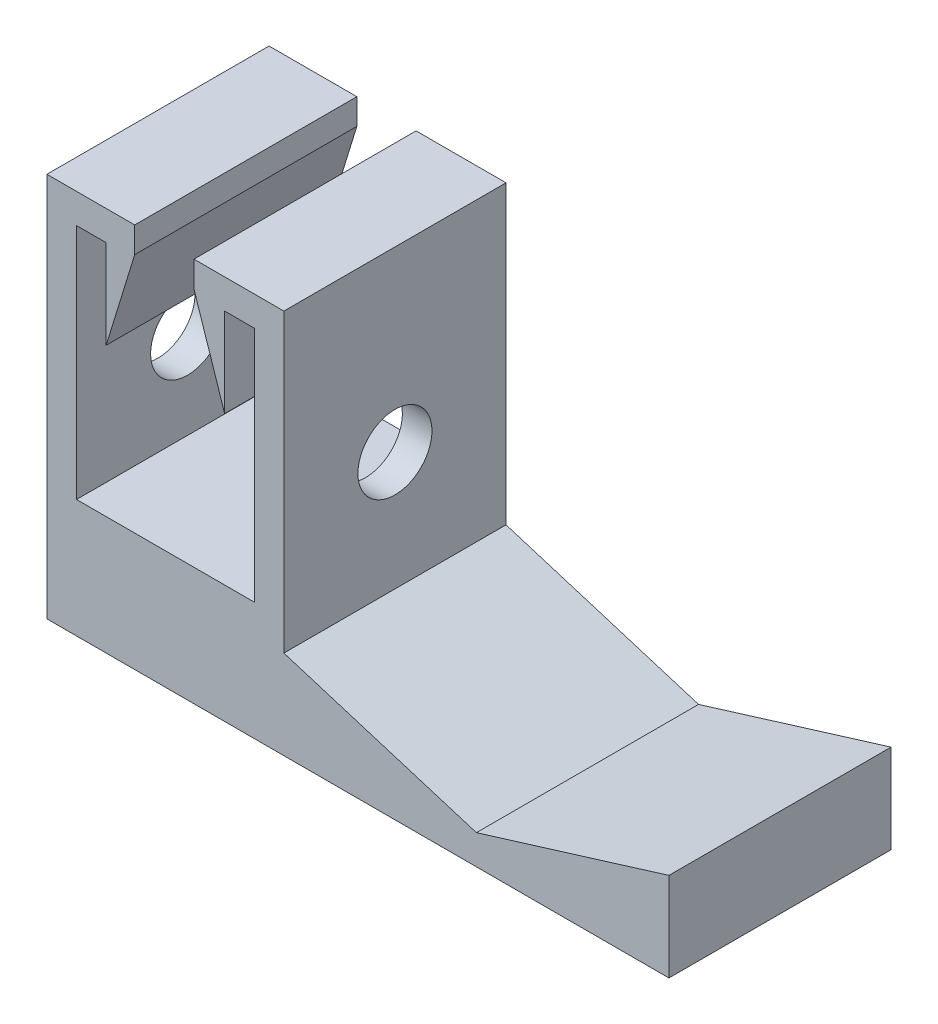
SolidWorks part; units mm, degrees
ref_plane "Front Plane" through (0, 0, 0) normal (0, 0, 1) x (1, 0, 0)
ref_plane "Top Plane" through (0, 0, 0) normal (0, 1, 0) x (1, 0, 0)
ref_plane "Right Plane" through (0, 0, 0) normal (1, 0, 0) x (0, 0, -1)
sketch "Sketch1" plane through (0, 0, 0) normal (0, 0, 1) x (1, 0, 0)
  line L0 (-105, 0) -> (105, 0)
  line L1 (-105, 0) -> (-105, 130)
  line L2 (105, 0) -> (105, 30)
  line L3 (105, 30) -> (40, 10)
  line L4 (40, 10) -> (-25, 30)
  line L5 (-25, 30) -> (-25, 130)
  line L6 (-25, 130) -> (-55.3655, 130)
  line L7 (-55.3655, 130) -> (-55.3655, 121.3121)
  line L8 (-55.3655, 121.3121) -> (-45, 90)
  line L9 (-45, 90) -> (-45, 120)
  line L10 (-45, 120) -> (-35, 120)
  line L11 (-35, 120) -> (-35, 39.9092)
  line L12 (-85, 120) -> (-95, 120)
  line L13 (-85, 90) -> (-85, 120)
  line L14 (-95, 120) -> (-85, 120)
  line L15 (-95, 120) -> (-95, 39.9092)
  line L16 (-85, 90) -> (-75.3655, 121.3121)
  line L17 (-75.3655, 121.3121) -> (-75.3655, 130)
  line L18 (-75.3655, 130) -> (-105, 130)
  line L19 (-95, 39.9092) -> (-35, 39.9092)
  point P4 (0, 0)
  point P8 (-40.1828, 130)
  point P22 (-55.3655, 125.656)
  dimension "D1" = 210
  dimension "D2" = 130
  dimension "D3" = 10
  dimension "D4" = 65
  dimension "D5" = 100
  dimension "D6" = 30
  dimension "D7" = 30
  dimension "D8" = 10
  dimension "D9" = 20
  dimension "D10" = 40
  dimension "D11" = 10
  dimension "D12" = 10
  dimension "D13" = 10
  dimension "D14" = 80
  dimension "D15" = 40
  dimension "D16" = 40
  dimension "D17" = 10
extrude "Boss-Extrude1" add sketch "Sketch1" along normal mid plane 75 contours L19 L15 L12 L13 L16 L17 L18 L1 L0 L2 L3 L4 L5 L6 L7 L8 L9 L10 L11
sketch "Sketch2" plane through (-105, 0, 0) normal (-1, 0, 0) x (0, 0, 1)
  line L0 (37.5, 0) -> (37.5, 130) construction
  line L1 (37.5, 0) -> (-37.5, 0) construction
  circle A0 centre (0, 70) radius 12.5
  dimension "D1" = 25
  dimension "D2" = 37.5
  dimension "D3" = 70
extrude "Cut-Extrude1" cut sketch "Sketch2" against normal blind 100 contours A0
